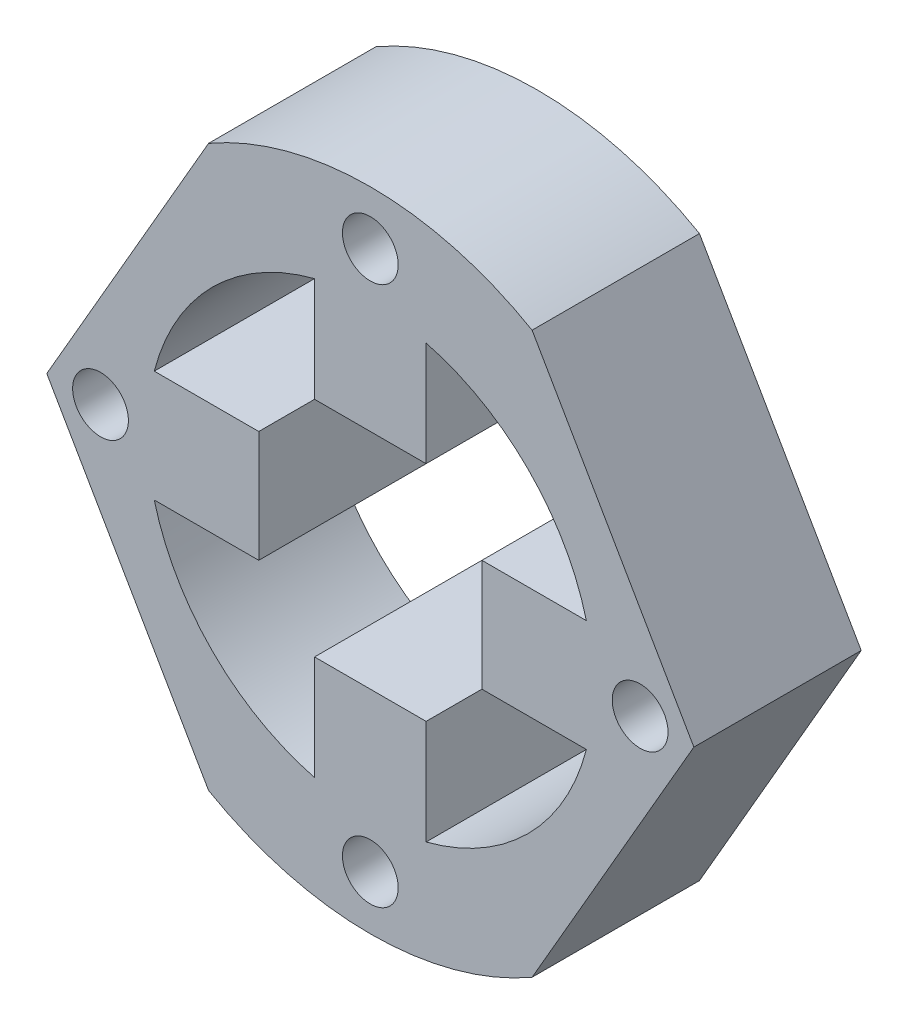
SolidWorks part; units mm, degrees
ref_plane "Front Plane" through (0, 0, 0) normal (0, 0, 1) x (1, 0, 0)
ref_plane "Top Plane" through (0, 0, 0) normal (0, 1, 0) x (1, 0, 0)
ref_plane "Right Plane" through (0, 0, 0) normal (1, 0, 0) x (0, 0, -1)
sketch "Sketch6" plane through (0, 0, 0) normal (0, 0, 1) x (1, 0, 0)
  circle A0 centre (0, 0) radius 20
  circle A1 centre (0, 0) radius 29
  dimension "D1" = 40
  dimension "D2" = 58
extrude "Inner Ring" add sketch "Sketch6" against normal blind 15 separate body
sketch "Sketch7" plane through (0, 0, 0) normal (0, 0, 1) x (1, 0, 0)
  line L2 (-10, 5) -> (-10, -5)
  line L3 (-5, 10) -> (5, 10)
  line L4 (10, 5) -> (10, -5)
  line L5 (-5, -10) -> (5, -10)
  line L14 (-19.3649, 5) -> (-10, 5)
  line L15 (-19.3649, -5) -> (-10, -5)
  line L16 (-5, 19.3649) -> (-5, 10)
  line L17 (5, 19.3649) -> (5, 10)
  line L18 (19.3649, 5) -> (10, 5)
  line L19 (19.3649, -5) -> (10, -5)
  line L20 (5, -19.3649) -> (5, -10)
  line L21 (-5, -19.3649) -> (-5, -10)
  circle A1 centre (0, 0) radius 20
  circle M19 centre (0, 0) radius 20
  dimension "D1" = 20
  dimension "D2" = 20
  dimension "D3" = 10
  dimension "D5" = 10
  dimension "D7" = 10
  dimension "D8" = 10
extrude "Motor Connector Cut" add sketch "Sketch7" against normal blind 15 contours L19 L18 L4 M19 | L17 L16 L3 M19 | L15 L2 L14 M19 | L21 L20 L5 M19
sketch "Sketch8" plane through (0, 0, 0) normal (0, 0, 1) x (1, 0, 0)
  circle A1 centre (0, 24.1825) radius 2.5
  circle A2 centre (24.1825, 0) radius 2.5
  circle A3 centre (0, -24.1825) radius 2.5
  circle A4 centre (-24.1825, 0) radius 2.5
  dimension "D1" = 5
  dimension "D2" = 5
  dimension "D3" = 5
  dimension "D4" = 5
  dimension "D6" = 48.3649
  dimension "D8" = 48.3649
extrude "M3 Holes" cut sketch "Sketch8" against normal blind 53 and the other way blind 38
sketch "Sketch9" plane through (0, 0, -15) normal (0, 0, -1) x (-1, 0, 0)
  line L1 (29, 0) -> (14.5, 25.1147)
  line L3 (-14.5, 25.1147) -> (-29, 0)
  line L4 (-29, 0) -> (-14.5, -25.1147)
  line L6 (14.5, -25.1147) -> (29, 0)
  line L7 (14.5, 25.1147) -> (0, 25.1147) [skipped]
  line L8 (0, -25.1147) -> (14.5, -25.1147) [skipped]
  circle A2 centre (0, 0) radius 29
  circle M28 centre (0, 0) radius 29
extrude "Cut-Extrude1" cut sketch "Sketch9" against normal blind 27 and the other way blind 16 contours L1 M28 | L3 M28 | L4 M28 | L6 M28
